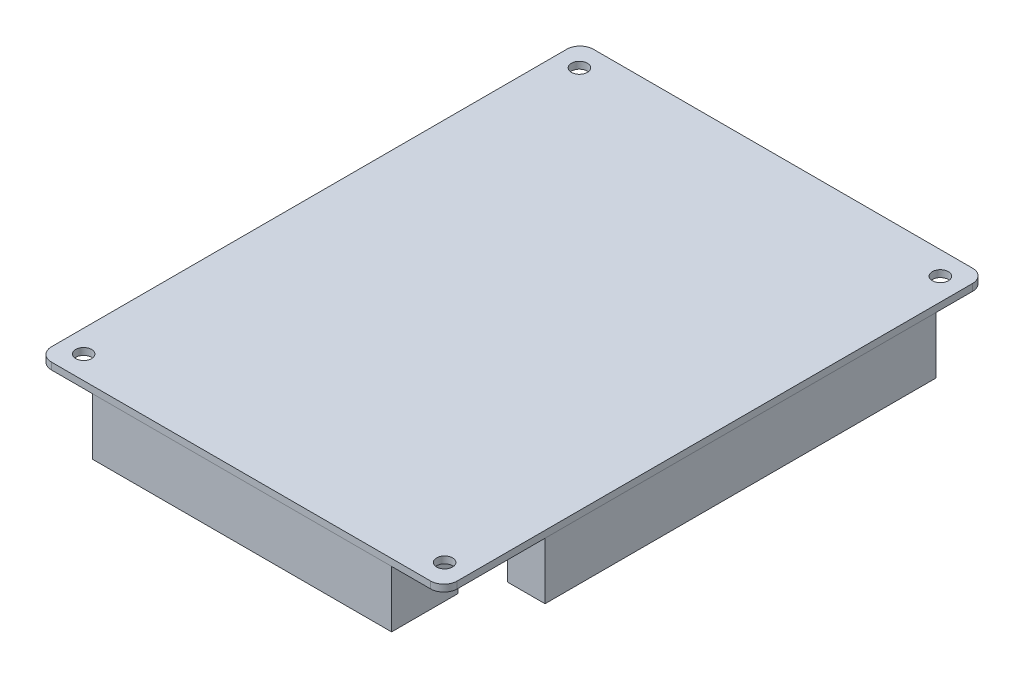
SolidWorks part; units mm, degrees
ref_plane "Front Plane" through (0, 0, 0) normal (0, 0, 1) x (1, 0, 0)
ref_plane "Top Plane" through (0, 0, 0) normal (0, 1, 0) x (1, 0, 0)
ref_plane "Right Plane" through (0, 0, 0) normal (1, 0, 0) x (0, 0, -1)
sketch "Sketch1" plane through (0, 0, 0) normal (0, 1, 0) x (1, 0, 0)
  line L1 (45.75, -61.1) -> (-45.75, -61.1)
  line L2 (45.75, -61.1) -> (45.75, 61.1)
  line L3 (45.75, 61.1) -> (-45.75, 61.1)
  line L4 (-45.75, -61.1) -> (-45.75, 61.1)
  line L5 (45.75, -61.1) -> (-45.75, 61.1) construction
  line L6 (45.75, 61.1) -> (-45.75, -61.1) construction
  point P0 (0, 0)
  dimension "D1" = 91.5
  dimension "D2" = 122.2
extrude "Boss-Extrude1" add sketch "Sketch1" along normal blind 1.5494
hole_wizard "M3 Clearance Hole1" positions "Sketch2" profile "Sketch3" hole size "M3" standard "ANSI Metric"
sketch "Sketch2" plane through (0, 1.5494, 0) normal (0, 1, 0) x (1, 0, 0)
  line L1 (40.7, -55.9) -> (-40.7, -55.9) construction
  line L2 (40.7, -55.9) -> (40.7, 55.9) construction
  line L3 (40.7, 55.9) -> (-40.7, 55.9) construction
  line L4 (-40.7, -55.9) -> (-40.7, 55.9) construction
  line L6 (40.7, 55.9) -> (-40.7, -55.9) construction
  point P2 (-40.7, 55.9)
  point P25 (40.7, -55.9)
  point P26 (40.7, 55.9)
  point P27 (-40.7, -55.9)
  dimension "D1" = 81.4
  dimension "D2" = 111.8
sketch "Sketch3" plane through (-40.7, 1.5494, -55.9) normal (1, 0, 0) x (0, 0, 1)
  line L0 (0, 0) -> (0, 12)
  line L1 (0, 12) -> (1.8, 12)
  line L2 (1.8, 12) -> (1.8, 0)
  line L5 (1.8, 0) -> (0, 0)
  line L10 (0, 12) -> (-1.8, 12) construction
  line L11 (0, -6.35) -> (0, 107.95) construction
  dimension "Hole Dia." = 3.6
  dimension "Hole Depth" = 12
  dimension "Drill Angle" = 180
fillet "Fillet1" radius 3 4 edges at (-45.75, 0.7747, -61.1) (45.75, 0.7747, -61.1) (45.75, 0.7747, 61.1) (-45.75, 0.7747, 61.1)
sketch "Sketch4" plane through (0, 0, 0) normal (0, -1, 0) x (1, 0, 0)
  line L0 (45.75, 58.1) -> (45.75, -58.1) construction
  line L1 (45.55, 38.1) -> (37.05, 38.1)
  line L2 (45.55, 38.1) -> (45.55, -50.1)
  line L3 (45.55, -50.1) -> (37.05, -50.1)
  line L4 (37.05, 38.1) -> (37.05, -50.1)
  line L5 (42.75, -61.1) -> (-42.75, -61.1) construction
  line L6 (18.75, -60.9) -> (-30.75, -60.9)
  line L7 (18.75, -60.9) -> (18.75, -53.4)
  line L8 (18.75, -53.4) -> (-30.75, -53.4)
  line L9 (-30.75, -60.9) -> (-30.75, -53.4)
  line L10 (-45.75, -58.1) -> (-45.75, 58.1) construction
  line L11 (-45.55, -50.1) -> (-37.05, -50.1)
  line L12 (-45.55, -50.1) -> (-45.55, 40.1)
  line L13 (-45.55, 40.1) -> (-37.05, 40.1)
  line L14 (-37.05, -50.1) -> (-37.05, 40.1)
  line L15 (-42.75, 61.1) -> (42.75, 61.1) construction
  line L16 (33.75, 60.9) -> (-33.75, 60.9)
  line L17 (33.75, 60.9) -> (33.75, 45.9)
  line L18 (33.75, 45.9) -> (-33.75, 45.9)
  line L19 (-33.75, 60.9) -> (-33.75, 45.9)
  point P24 (0, 0)
  dimension "D1" = 15
  dimension "D2" = 12
  dimension "D3" = 12
  dimension "D4" = 23
  dimension "D5" = 11
  dimension "D6" = 7.5
  dimension "D7" = 27
  dimension "D8" = 15
  dimension "D9" = 11
  dimension "D10" = 21
  dimension "D11" = 8.5
  dimension "D12" = 8.5
  dimension "D13" = 0.2
  dimension "D14" = 0.2
  dimension "D15" = 0.2
  dimension "D16" = 0.2
extrude "Boss-Extrude2" add sketch "Sketch4" along normal blind 13
